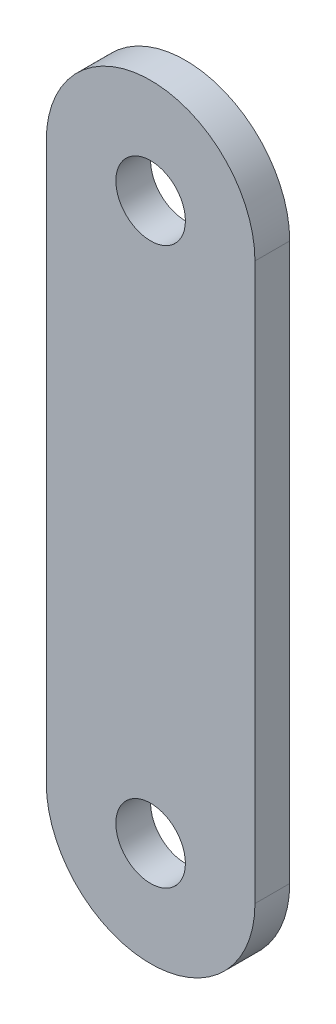
SolidWorks part; units mm, degrees
ref_plane "Front Plane" through (0, 0, 0) normal (0, 0, 1) x (1, 0, 0)
ref_plane "Top Plane" through (0, 0, 0) normal (0, 1, 0) x (1, 0, 0)
ref_plane "Right Plane" through (0, 0, 0) normal (1, 0, 0) x (0, 0, -1)
sketch "Sketch2" plane through (0, 0, 0) normal (0, 0, 1) x (1, 0, 0)
  line L2 (-9.525, 25.4) -> (-9.525, -25.4)
  line L4 (9.525, 25.4) -> (9.525, -25.4)
  circle A0 centre (0, 25.4) radius 3.175
  circle A1 centre (0, -25.4) radius 3.175
  arc A6 (9.525, 25.4) -> (-9.525, 25.4) centre (0, 25.4) ccw
  arc A7 (-9.525, -25.4) -> (9.525, -25.4) centre (0, -25.4) ccw
  point P0 (0, 0)
  point P4 (9.525, 0)
  dimension "D1" = 50.8
  dimension "D2" = 9.525
  dimension "D4" = 6.35
extrude "Boss-Extrude1" add sketch "Sketch2" along normal mid plane 3.175 contours L2 A7 L4 A6 A0 A1
